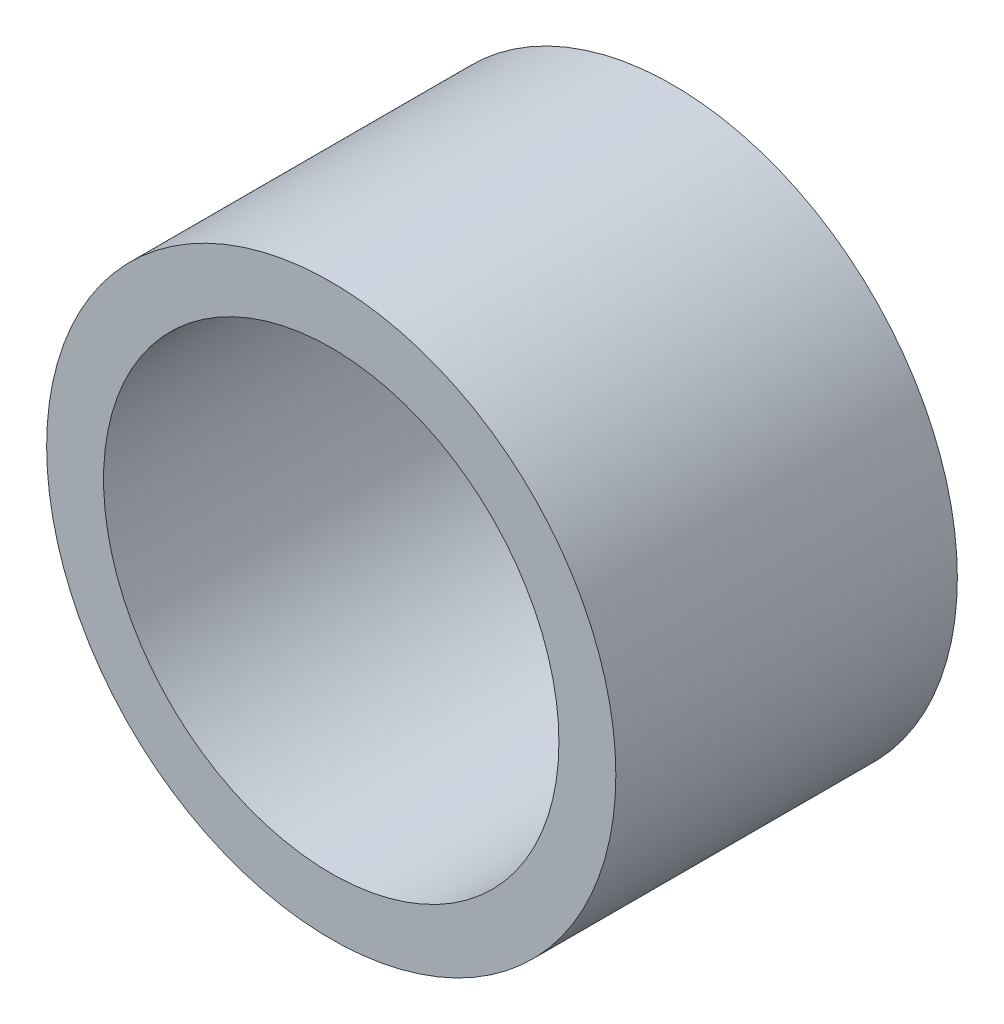
SolidWorks part; units mm, degrees
material "PTFE (general)"
ref_plane "Front Plane" through (0, 0, 0) normal (0, 0, 1) x (1, 0, 0)
ref_plane "Top Plane" through (0, 0, 0) normal (0, 1, 0) x (1, 0, 0)
ref_plane "Right Plane" through (0, 0, 0) normal (1, 0, 0) x (0, 0, -1)
sketch "Sketch1" plane through (0, 0, 0) normal (0, 0, 1) x (1, 0, 0)
  circle A0 centre (0, 0) radius 7.9375
  circle A1 centre (0, 0) radius 6.35
  dimension "D1" = 15.875
  dimension "ID" = 12.7
extrude "Extrude1" add sketch "Sketch1" along normal mid plane 9.525
sketch "Sketch2" plane through (0, 0, 0) normal (1, 0, 0) x (0, 0, -1)
  line L0 (-4.7625, -6.35) -> (4.7625, -6.35) construction
  line L3 (4.7625, 6.35) -> (-4.7625, 6.35) construction
  line L5 (-4.7625, -6.35) -> (4.7625, -6.35)
  line L6 (4.7625, 6.35) -> (-4.7625, 6.35)
sketch "Sketch4" plane through (0, 0, 4.7625) normal (0, 0, 1) x (1, 0, 0)
  line L0 (0, 0) -> (-4.4901, 4.4901)
  line L1 (0, -24.4475) -> (0, 24.4475) construction
  circle A0 centre (0, 0) radius 6.35 construction
  dimension "D1" = 45
